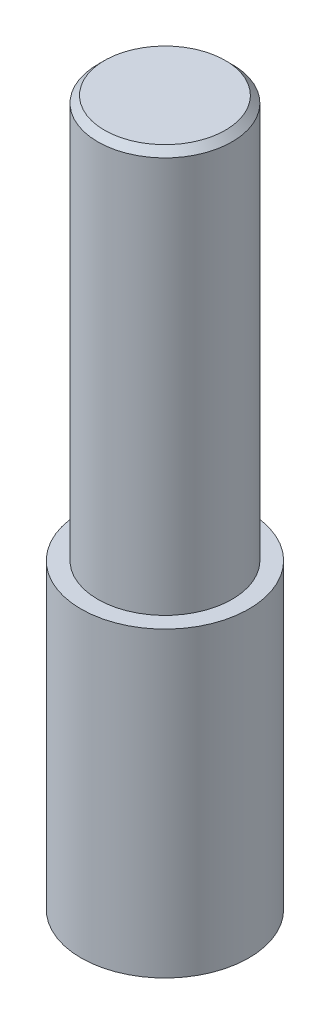
SolidWorks part; units mm, degrees
material "Plain Carbon Steel"
ref_plane "Front Plane" through (0, 0, 0) normal (0, 0, 1) x (1, 0, 0)
ref_plane "Top Plane" through (0, 0, 0) normal (0, 1, 0) x (1, 0, 0)
ref_plane "Right Plane" through (0, 0, 0) normal (1, 0, 0) x (0, 0, -1)
sketch "Sketch1" plane through (0, 0, 0) normal (0, 1, 0) x (1, 0, 0)
  circle A0 centre (0, 0) radius 12.5
  dimension "D1" = 25
extrude "Boss-Extrude1" add sketch "Sketch1" along normal blind 45
ref_plane "Plane1" through (0, 45, 0) normal (0, 1, 0) x (1, 0, 0)
sketch "Sketch2" plane through (0, 45, 0) normal (0, 1, 0) x (1, 0, 0)
  circle A0 centre (0, 0) radius 10
  dimension "D1" = 20
extrude "Boss-Extrude2" add sketch "Sketch2" along normal blind 60
chamfer "Chamfer1" distance 1 angle 45 1 edges at (0, 105, 10)
